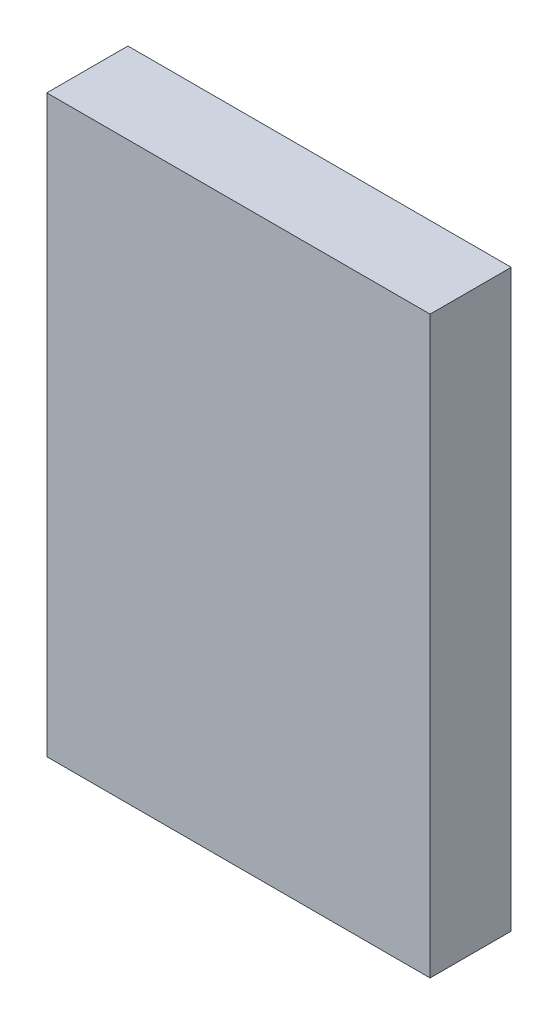
SolidWorks part; units mm, degrees
material "Balsa"
ref_plane "Front Plane" through (0, 0, 0) normal (0, 0, 1) x (1, 0, 0)
ref_plane "Top Plane" through (0, 0, 0) normal (0, 1, 0) x (1, 0, 0)
ref_plane "Right Plane" through (0, 0, 0) normal (1, 0, 0) x (0, 0, -1)
sketch "Sketch1" plane through (0, 0, 0) normal (0, 0, 1) x (1, 0, 0)
  line L1 (0, 0) -> (30, 0)
  line L2 (0, 0) -> (0, 45)
  line L3 (0, 45) -> (30, 45)
  line L4 (30, 0) -> (30, 45)
  dimension "D1" = 30
  dimension "D2" = 45
extrude "Boss-Extrude1" add sketch "Sketch1" along normal blind 6.35
